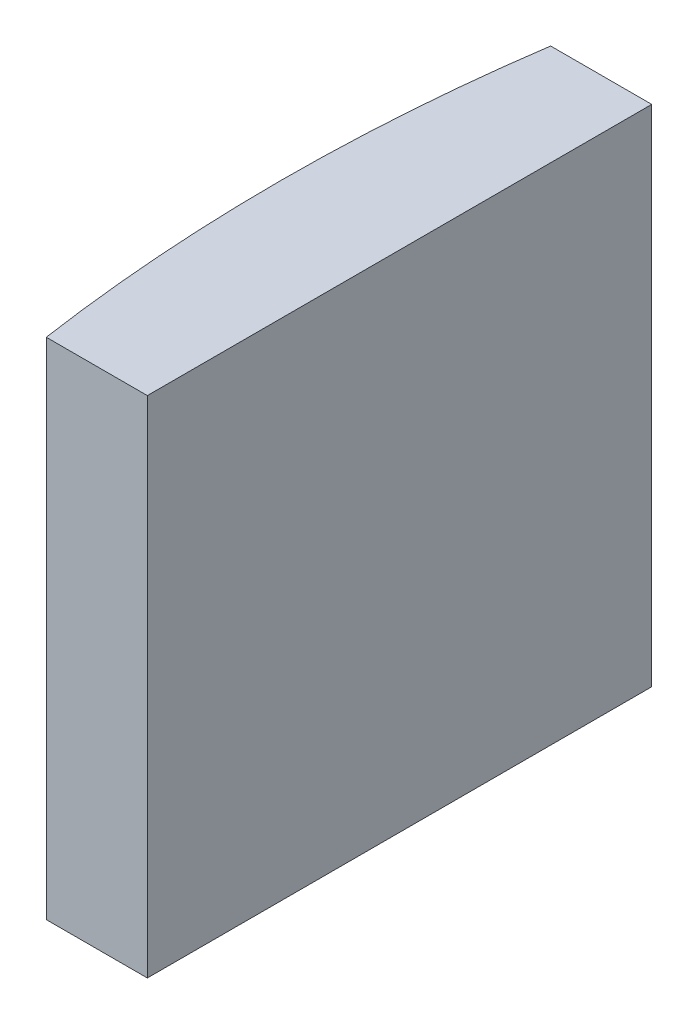
SolidWorks part; units mm, degrees
ref_plane "前视基准面" through (0, 0, 0) normal (0, 0, 1) x (1, 0, 0)
ref_plane "上视基准面" through (0, 0, 0) normal (0, 1, 0) x (1, 0, 0)
ref_plane "右视基准面" through (0, 0, 0) normal (1, 0, 0) x (0, 0, -1)
sketch "草图1" plane through (0, 0, 0) normal (0, 1, 0) x (1, 0, 0)
  line L0 (-34.9849, 0) -> (10.8051, 0) construction
  line L1 (-29.6289, 5) -> (-27.6248, 5)
  line L2 (-29.6289, -5) -> (-27.6248, -5)
  line L3 (-27.6248, 5) -> (-27.6248, -5)
  arc A0 (-29.6289, 5) -> (-29.6289, -5) centre (4.3552, 0) ccw
  point P2 (-29.9948, 0)
  point P4 (-27.6248, 0)
  point P8 (-34.9849, 0)
  dimension "D2" = 5
  dimension "D3" = 34.35
  dimension "D4" = 2.37
  dimension "D1" = 5
extrude "凸台-拉伸1" add sketch "草图1" along normal blind 10
